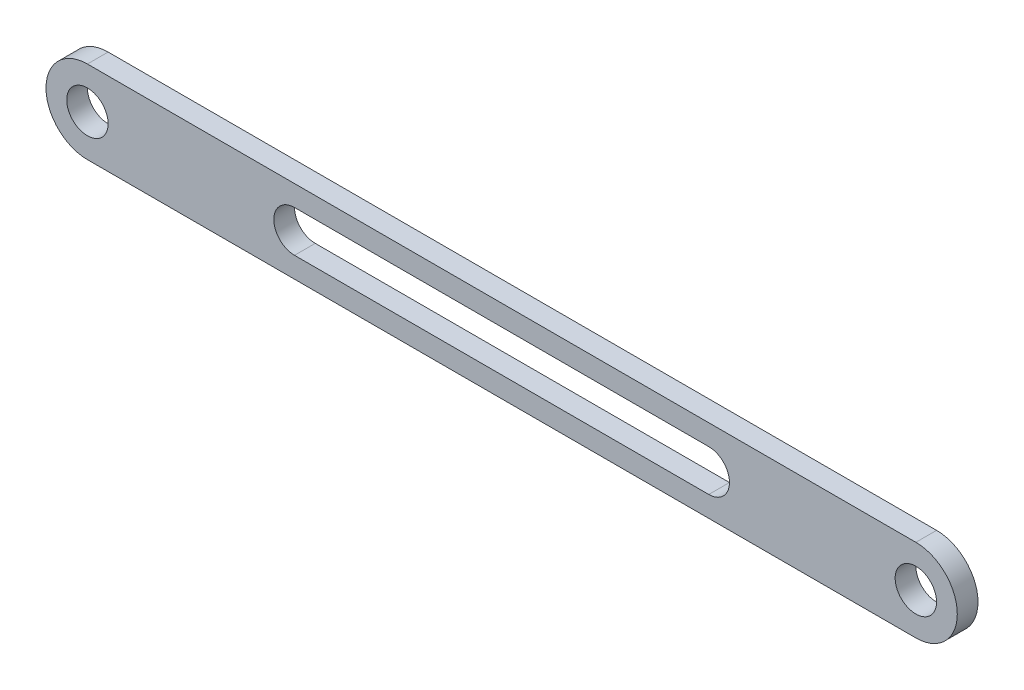
SolidWorks part; units mm, degrees
ref_plane "Front Plane" through (0, 0, 0) normal (0, 0, 1) x (1, 0, 0)
ref_plane "Top Plane" through (0, 0, 0) normal (0, 1, 0) x (1, 0, 0)
ref_plane "Right Plane" through (0, 0, 0) normal (1, 0, 0) x (0, 0, -1)
sketch "Sketch1" plane through (0, 0, 0) normal (0, 0, 1) x (1, 0, 0)
  line L0 (-89.5193, 0) -> (310.4807, 0) construction
  line L1 (-89.5193, 20) -> (310.4807, 20)
  line L2 (-89.5193, -20) -> (310.4807, -20)
  line L3 (10.4807, 0) -> (210.4807, 0) construction
  line L4 (10.4807, 10) -> (210.4807, 10)
  line L5 (10.4807, -10) -> (210.4807, -10)
  arc A0 (-89.5193, 20) -> (-89.5193, -20) centre (-89.5193, 0) ccw
  arc A1 (310.4807, -20) -> (310.4807, 20) centre (310.4807, 0) ccw
  arc A2 (10.4807, 10) -> (10.4807, -10) centre (10.4807, 0) ccw
  arc A3 (210.4807, -10) -> (210.4807, 10) centre (210.4807, 0) ccw
  circle A4 centre (-89.5193, 0) radius 10
  circle A5 centre (310.4807, 0) radius 10
  point P1 (110.4807, 0)
  point P10 (110.4807, 0)
extrude "Boss-Extrude1" add sketch "Sketch1" along normal blind 10
